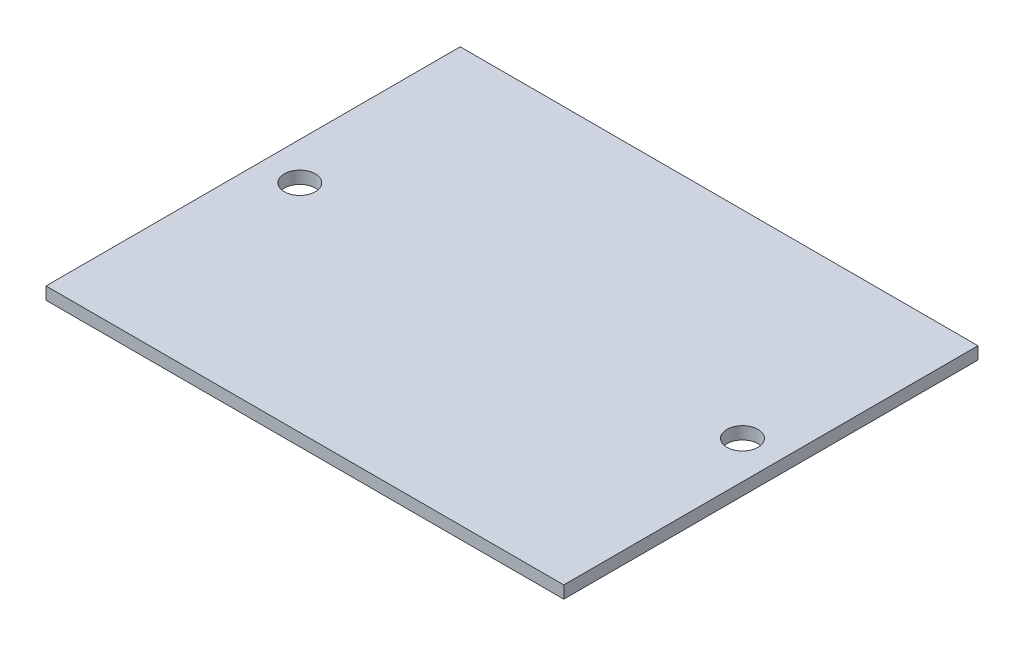
SolidWorks part; units mm, degrees
ref_plane "Front" through (0, 0, 0) normal (0, 0, 1) x (1, 0, 0)
ref_plane "Top" through (0, 0, 0) normal (0, 1, 0) x (1, 0, 0)
ref_plane "Right" through (0, 0, 0) normal (1, 0, 0) x (0, 0, -1)
sketch "Sketch1" plane through (0, 0, 0) normal (0, 1, 0) x (1, 0, 0)
  line L0 (18.125, 104.4097) -> (231.875, 104.4097) construction
  line L1 (0, 0) -> (250, 0)
  line L2 (0, 0) -> (0, 200)
  line L3 (0, 200) -> (250, 200)
  line L4 (250, 0) -> (250, 200)
  circle A0 centre (18.125, 104.4097) radius 7.5
  circle A1 centre (231.875, 104.4097) radius 7.5
  point P9 (125, 104.4097)
  point P10 (125, 200)
  dimension "D4" = 15
  dimension "D1" = 200
  dimension "D2" = 250
  dimension "D3" = 213.75
extrude "Boss-Extrude1" add sketch "Sketch1" along normal blind 5.9944
equation "\"ABS_thickness_1/16\" = 1.524\t"
equation "\"ABS_thickness_3/32\" = 2.3622"
equation "\"ABS_thickness_1/8\" = 2.9972\t"
equation "\"ABS_thickness_1/4\" = 5.9944"
equation "\"Bus_bar_thickness\" = 3.175"
equation "\"Connector_width\" = 20.2"
equation "\"Number_of_cells_long\" = 25"
equation "\"Number_of_cells_wide\" = 2"
equation "\"Cell_height\" = 65.0"
equation "\"Cell_diam\" = 18.0"
equation "\"Enclosure_Width\" = 292"
equation "\"Enclosure_Length\" = 260"
equation "\"Enclosure_Height\" = 515"
equation "\"D1@Boss-Extrude1\"=\"ABS_thickness_1/4\""
